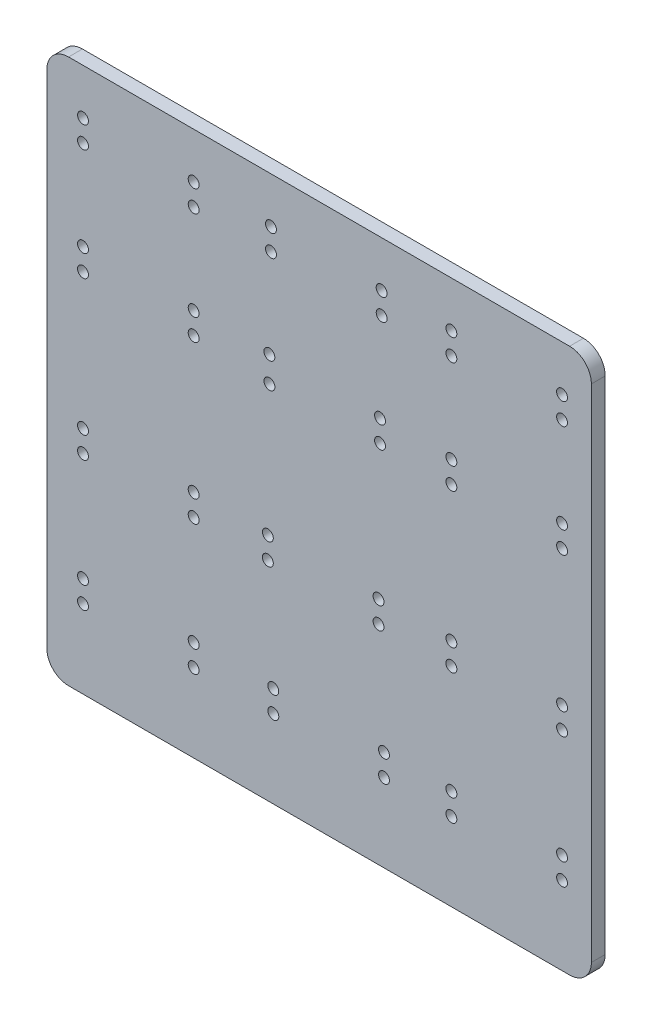
SolidWorks part; units mm, degrees
ref_plane "Front Plane" through (0, 0, 0) normal (0, 0, 1) x (1, 0, 0)
ref_plane "Top Plane" through (0, 0, 0) normal (0, 1, 0) x (1, 0, 0)
ref_plane "Right Plane" through (0, 0, 0) normal (1, 0, 0) x (0, 0, -1)
sketch "Sketch1" plane through (-15.0183, 0, 0) normal (0, 0, 1) x (1, 0, 0)
  line L1 (-49.8295, 208.3661) -> (200.1705, 208.3661)
  line L2 (-49.8295, 208.3661) -> (-49.8295, -41.6339)
  line L3 (-49.8295, -41.6339) -> (200.1705, -41.6339)
  line L4 (200.1705, 208.3661) -> (200.1705, -41.6339)
extrude "Boss-Extrude1" add sketch "Sketch1" along normal blind 6.35
fillet "Fillet1" radius 10 4 edges at (-64.8478, 208.3661, 3.175) (-64.8478, -41.6339, 3.175) (185.1522, -41.6339, 3.175) (185.1522, 208.3661, 3.175)
sketch "Sketch3" plane through (-15.0183, 0, 6.35) normal (0, 0, 1) x (1, 0, 0)
  circle A0 centre (52.3461, 136.2456) radius 5
  circle A1 centre (103.1461, 136.2456) radius 5
  circle A2 centre (103.1461, 126.2456) radius 5
  circle A3 centre (52.3776, 124.4577) radius 5
  point P8 (0, 0)
  point P9 (0, 0)
  dimension "D1" = 50.8
  dimension "D2" = 50.8
  dimension "D3" = 10
hole_wizard "Tap Drill for M6x1.0 Tap1" positions "Sketch4" profile "Sketch6" hole size "M6x1.0" standard "ANSI Metric" end condition through all
sketch "Sketch4" plane through (0, 0, 6.35) normal (0, 0, 1) x (1, 0, 0)
  point P0 (37.3278, 136.2456)
  point P3 (88.1278, 136.2456)
  point P6 (37.3593, 124.4577)
  point P9 (88.1278, 126.2456)
sketch "Sketch6" plane through (37.3278, 136.2456, 6.35) normal (1, 0, 0) x (0, -1, 0)
  line L0 (0, 0) -> (0, 6.35)
  line L1 (0, 6.35) -> (2.5, 6.35)
  line L2 (2.5, 6.35) -> (2.5, 0)
  line L5 (2.5, 0) -> (0, 0)
  line L11 (0, -6.35) -> (0, 107.95) construction
  dimension "Thru Hole Dia." = 5
  dimension "Thru Hole Depth" = 6.35
sketch "Sketch22" plane through (-15.0183, 0, 6.35) normal (0, 0, 1) x (1, 0, 0)
  circle A8 centre (-33.2103, 187.3752) radius 3.8675
  circle A9 centre (17.5897, 187.3752) radius 3.9331
  circle A10 centre (17.5897, 177.3752) radius 2.5029
  circle A11 centre (-33.2103, 177.3752) radius 4.2906
  circle A12 centre (135.9109, 187.3752) radius 5.0057
  circle A13 centre (186.7109, 187.3752) radius 5.0817
  circle A14 centre (186.7109, 177.3752) radius 5.0817
  circle A15 centre (135.9109, 177.3752) radius 5.2792
  circle A16 centre (-33.2103, 64.0205) radius 5.1567
  circle A18 centre (17.5897, 64.0205) radius 6.366
  circle A19 centre (17.5897, 54.0205) radius 5.8643
  circle A20 centre (-33.2103, 54.0205) radius 5.5851
  circle A21 centre (135.9109, 64.0205) radius 6.7462
  circle A22 centre (186.7109, 64.0205) radius 6.1515
  circle A23 centre (186.7109, 54.0205) radius 4.8103
  circle A24 centre (135.9109, 54.0205) radius 5.6534
  circle A25 centre (-33.2103, 4.3096) radius 5.6534
  circle A26 centre (17.5897, 4.3096) radius 5.7208
  circle A27 centre (135.9109, 4.3096) radius 6.0784
  circle A28 centre (186.7109, 4.3096) radius 6.9054
  circle A29 centre (186.7109, -5.6904) radius 5.2792
  circle A30 centre (135.9109, -5.6904) radius 6.3257
  circle A31 centre (17.5897, -5.6904) radius 4.2906
  circle A32 centre (-33.2103, -5.6904) radius 3.218
  circle A33 centre (-33.2103, 136.2456) radius 4.3547
  circle A34 centre (17.5897, 136.2456) radius 4.673
  circle A35 centre (17.5897, 126.2456) radius 2.6727
  circle A36 centre (-33.2103, 126.2456) radius 3.3009
  circle A37 centre (135.9109, 136.2456) radius 3.5292
  circle A38 centre (186.7109, 136.2456) radius 4.6367
  circle A39 centre (135.9109, 126.2456) radius 4.2076
  circle A40 centre (186.7109, 126.2456) radius 3.3702
  point P0 (0, 0)
  dimension "D7" = 50.8
  dimension "D8" = 10
  dimension "D9" = 50.8
  dimension "D10" = 50.8
  dimension "D11" = 10
  dimension "D12" = 50.8
  dimension "D13" = 50.8
  dimension "D14" = 50.8
  dimension "D15" = 50.8
  dimension "D16" = 50.8
  dimension "D17" = 50.8
  dimension "D18" = 50.8
  dimension "D19" = 50.8
  dimension "D20" = 10
  dimension "D21" = 10
  dimension "D22" = 10
  dimension "D23" = 10
  dimension "D24" = 10
  dimension "D25" = 10
  dimension "D26" = 10
  dimension "D27" = 10
  dimension "D30" = 10
  dimension "D31" = 10
  dimension "D32" = 50.8
  dimension "D33" = 10
  dimension "D34" = 10
  dimension "D35" = 50.8
  dimension "D36" = 10
hole_wizard "Tap Drill for M6x1.0 Tap2" positions "Sketch23" profile "Sketch24" hole size "M6x1.0" standard "ANSI Metric" end condition through all
sketch "Sketch23" plane through (0, 0, 6.35) normal (0, 0, 1) x (1, 0, 0)
  point P24 (120.8926, 187.3752)
  point P27 (171.6926, 187.3752)
  point P30 (171.6926, 177.3752)
  point P33 (120.8926, 177.3752)
  point P36 (-48.2286, 187.3752)
  point P39 (2.5714, 187.3752)
  point P42 (2.5714, 177.3752)
  point P45 (-48.2286, 177.3752)
  point P48 (-48.2286, 64.0205)
  point P51 (-48.2286, 54.0205)
  point P54 (2.5714, 64.0205)
  point P57 (2.5714, 54.0205)
  point P60 (2.5714, 4.3096)
  point P63 (2.5714, -5.6904)
  point P66 (-48.2286, 4.3096)
  point P69 (-48.2286, -5.6904)
  point P72 (120.8926, 64.0205)
  point P75 (171.6926, 64.0205)
  point P78 (171.6926, 54.0205)
  point P81 (120.8926, 54.0205)
  point P84 (120.8926, 4.3096)
  point P87 (171.6926, 4.3096)
  point P90 (171.6926, -5.6904)
  point P93 (120.8926, -5.6904)
  point P97 (-48.2286, 136.2456)
  point P100 (-48.2286, 126.2456)
  point P103 (2.5714, 136.2456)
  point P106 (2.5714, 126.2456)
  point P109 (120.8926, 136.2456)
  point P112 (120.8926, 126.2456)
  point P115 (171.6926, 136.2456)
  point P118 (171.6926, 126.2456)
  point P135 (0, 0)
  point P136 (0, 0)
  point P137 (0, 0)
  point P138 (0, 0)
  point P139 (0, 0)
sketch "Sketch24" plane through (120.8926, 187.3752, 6.35) normal (1, 0, 0) x (0, -1, 0)
  line L0 (0, 0) -> (0, 6.35)
  line L1 (0, 6.35) -> (2.5, 6.35)
  line L2 (2.5, 6.35) -> (2.5, 0)
  line L5 (2.5, 0) -> (0, 0)
  line L11 (0, -6.35) -> (0, 107.95) construction
  dimension "Thru Hole Dia." = 5
  dimension "Thru Hole Depth" = 6.35
sketch "Sketch32" plane through (-15.0183, 0, 6.35) normal (0, 0, 1) x (1, 0, 0)
  point P0 (53.0833, 187.3752)
  point P1 (0, 0)
  point P2 (0, 0)
  point P3 (103.8833, 187.3752)
  point P6 (53.0934, 177.3753)
  point P9 (103.8934, 177.3753)
  dimension "D1" = 50.8
  dimension "D2" = 10
  dimension "D3" = 10
  dimension "D4" = 50.8
sketch "Sketch33" plane through (-15.0183, 0, 6.35) normal (0, 0, 1) x (1, 0, 0)
  point P0 (51.6604, 64.0205)
  point P1 (0, 0)
  point P2 (0, 0)
  point P3 (102.4604, 64.0205)
  point P6 (51.6548, 54.0205)
  point P9 (102.4548, 54.0205)
  dimension "D1" = 50.8
  dimension "D2" = 10
  dimension "D3" = 10
  dimension "D4" = 50.8
sketch "Sketch34" plane through (-15.0183, 0, 6.35) normal (0, 0, 1) x (1, 0, 0)
  point P0 (54.1498, 4.3096)
  point P1 (0, 0)
  point P2 (0, 0)
  point P3 (104.9498, 4.3096)
  point P6 (54.1724, -5.6904)
  point P9 (104.9724, -5.6904)
  dimension "D1" = 50.8
  dimension "D2" = 50.8
  dimension "D3" = 10
  dimension "D4" = 10
hole_wizard "Tap Drill for M6x1.0 Tap3" positions "Sketch35" profile "Sketch36" hole size "M6x1.0" standard "ANSI Metric" end condition through all
sketch "Sketch35" plane through (0, 0, 6.35) normal (0, 0, 1) x (1, 0, 0)
  point P12 (38.065, 187.3752)
  point P15 (88.865, 187.3752)
  point P18 (88.8751, 177.3753)
  point P21 (38.0751, 177.3753)
  point P24 (36.6421, 64.0205)
  point P27 (87.4421, 64.0205)
  point P30 (87.4365, 54.0205)
  point P33 (36.6365, 54.0205)
  point P36 (39.1314, 4.3096)
  point P39 (89.9314, 4.3096)
  point P42 (89.9541, -5.6904)
  point P45 (39.1541, -5.6904)
  point P48 (0, 0)
  point P49 (0, 0)
  point P50 (0, 0)
  point P51 (0, 0)
  point P52 (0, 0)
  point P53 (0, 0)
  point P54 (0, 0)
sketch "Sketch36" plane through (38.065, 187.3752, 6.35) normal (1, 0, 0) x (0, -1, 0)
  line L0 (0, 0) -> (0, 6.35)
  line L1 (0, 6.35) -> (2.5, 6.35)
  line L2 (2.5, 6.35) -> (2.5, 0)
  line L5 (2.5, 0) -> (0, 0)
  line L11 (0, -6.35) -> (0, 107.95) construction
  dimension "Thru Hole Dia." = 5
  dimension "Thru Hole Depth" = 6.35
